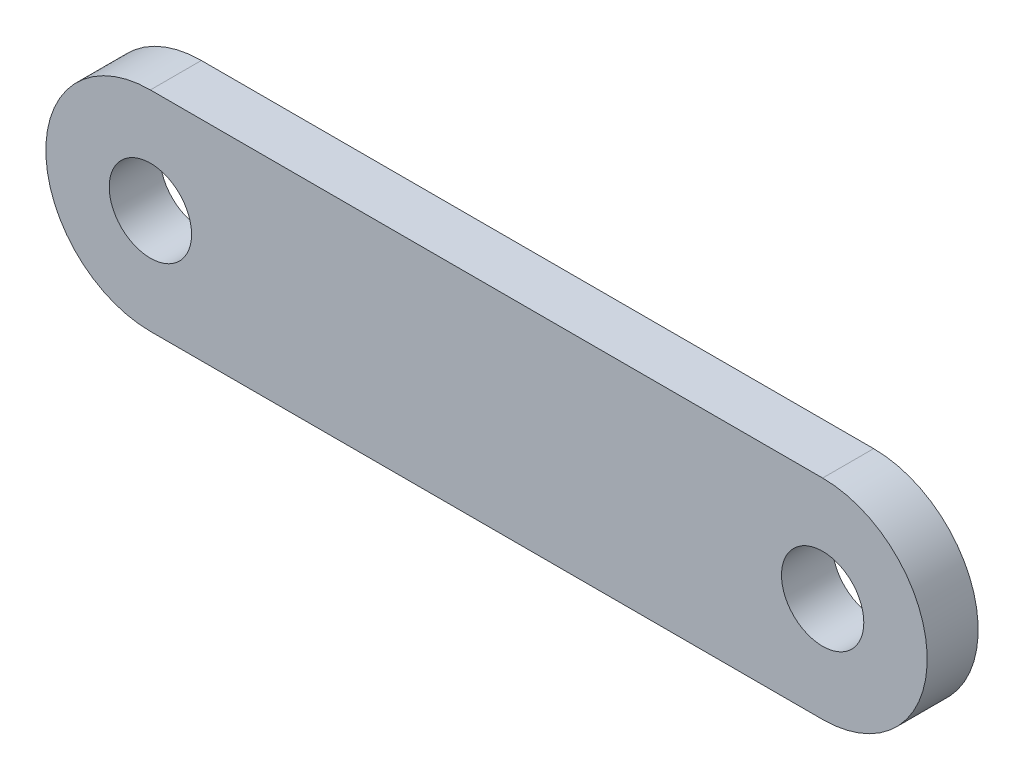
SolidWorks part; units mm, degrees
ref_plane "Front Plane" through (0, 0, 0) normal (0, 0, 1) x (1, 0, 0)
ref_plane "Top Plane" through (0, 0, 0) normal (0, 1, 0) x (1, 0, 0)
ref_plane "Right Plane" through (0, 0, 0) normal (1, 0, 0) x (0, 0, -1)
sketch "Sketch1" plane through (0, 0, 0) normal (0, 0, 1) x (1, 0, 0)
  line L0 (25.7175, 0) -> (-25.7175, 0) construction
  line L1 (25.7175, -8) -> (-25.7175, -8)
  line L2 (25.7175, 8) -> (-25.7175, 8)
  arc A0 (25.7175, -8) -> (25.7175, 8) centre (25.7175, 0) ccw
  arc A1 (-25.7175, 8) -> (-25.7175, -8) centre (-25.7175, 0) ccw
  circle A2 centre (25.7175, 0) radius 3.15
  circle A3 centre (-25.7175, 0) radius 3.15
  point P2 (0, 0)
  dimension "D3" = 6.3
  dimension "D1" = 16
  dimension "D2" = 51.435
extrude "Boss-Extrude1" add sketch "Sketch1" along normal blind 3.9
move or copy body "Body-Move/Copy1" [suppressed] bodies to move or copy 101
